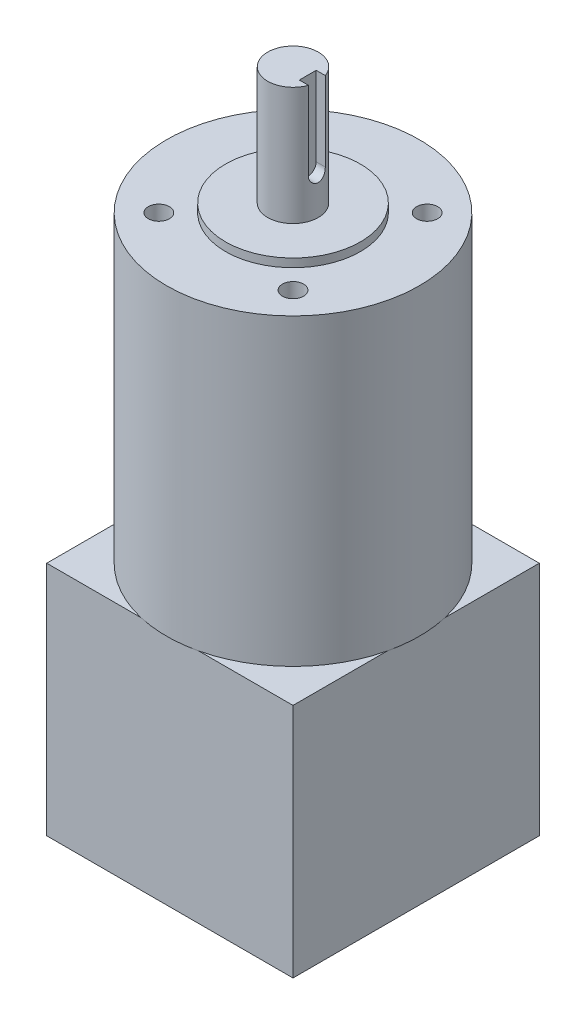
SolidWorks part; units mm, degrees
ref_plane "Front Plane" through (0, 0, 0) normal (0, 0, 1) x (1, 0, 0)
ref_plane "Top Plane" through (0, 0, 0) normal (0, 1, 0) x (1, 0, 0)
ref_plane "Right Plane" through (0, 0, 0) normal (1, 0, 0) x (0, 0, -1)
sketch "Sketch1" plane through (0, 0, 0) normal (0, 1, 0) x (1, 0, 0)
  line L1 (-29.21, -29.21) -> (29.21, -29.21)
  line L2 (-29.21, -29.21) -> (-29.21, 29.21)
  line L3 (-29.21, 29.21) -> (29.21, 29.21)
  line L4 (29.21, -29.21) -> (29.21, 29.21)
  line L5 (-29.21, -29.21) -> (29.21, 29.21) construction
  line L6 (-29.21, 29.21) -> (29.21, -29.21) construction
  point P0 (0, 0)
  dimension "D1" = 58.42
  dimension "D2" = 58.42
extrude "Boss-Extrude1" add sketch "Sketch1" along normal blind 56
sketch "Sketch2" plane through (0, 56, 0) normal (0, 1, 0) x (1, 0, 0)
  circle A0 centre (0, 0) radius 30
  dimension "D1" = 60
extrude "Boss-Extrude2" add sketch "Sketch2" along normal blind 72
sketch "Sketch3" plane through (0, 128, 0) normal (0, 1, 0) x (1, 0, 0)
  circle A0 centre (0, 0) radius 6
  dimension "D1" = 12
extrude "Boss-Extrude3" add sketch "Sketch3" along normal blind 30
sketch "Sketch4" plane through (0, 128, 0) normal (0, 1, 0) x (1, 0, 0)
  line L0 (0, 0) -> (0, 40.4963) construction
  line L1 (0, 0) -> (-37.1126, 37.1126) construction
  line L2 (0, 0) -> (40.6269, 0) construction
  circle A0 centre (0, 0) radius 16 construction
  circle A1 centre (0, 0) radius 22.5 construction
  circle A2 centre (-15.9099, 15.9099) radius 2.5
  circle A3 centre (0, 0) radius 22.5 construction
  circle A4 centre (15.9099, 15.9099) radius 2.5
  circle A5 centre (15.9099, -15.9099) radius 2.5
  circle A6 centre (-15.9099, -15.9099) radius 2.5
  dimension "D1" = 32
  dimension "D3" = 5
  dimension "D5" = 45
  dimension "D4" = 45
extrude "Cut-Extrude1" cut sketch "Sketch4" against normal blind 25.4
sketch "Sketch5" plane through (0, 158, 0) normal (0, 1, 0) x (1, 0, 0)
  line L1 (6, 2) -> (3.5, 2)
  line L2 (6, 2) -> (6, -2)
  line L3 (6, -2) -> (3.5, -2)
  line L4 (3.5, 2) -> (3.5, -2)
  line L5 (6, 2) -> (3.5, -2) construction
  line L6 (6, -2) -> (3.5, 2) construction
  circle A1 centre (0, 0) radius 6 construction
  circle A2 centre (0, 0) radius 6 construction
  point P0 (4.75, 0)
  point P5 (-6, 0)
  dimension "D1" = 4
  dimension "D2" = 2.5
  dimension "D3" = 9.5
extrude "Cut-Extrude2" cut sketch "Sketch5" against normal blind 18.8
sketch "Sketch6" plane through (0, 128, 0) normal (0, 1, 0) x (1, 0, 0)
  circle A0 centre (0, 0) radius 16
  dimension "D1" = 32
extrude "Boss-Extrude4" add sketch "Sketch6" along normal blind 2
sketch "Sketch7" plane through (3.5, 0, 0) normal (1, 0, 0) x (0, 0, -1)
  line L0 (2, 139.2) -> (-2, 139.2) construction
  line L1 (2, 139.2) -> (-2, 139.2)
  arc A0 (-2, 139.2) -> (2, 139.2) centre (0, 139.2) ccw
extrude "Cut-Extrude3" cut sketch "Sketch7" along normal up to next
